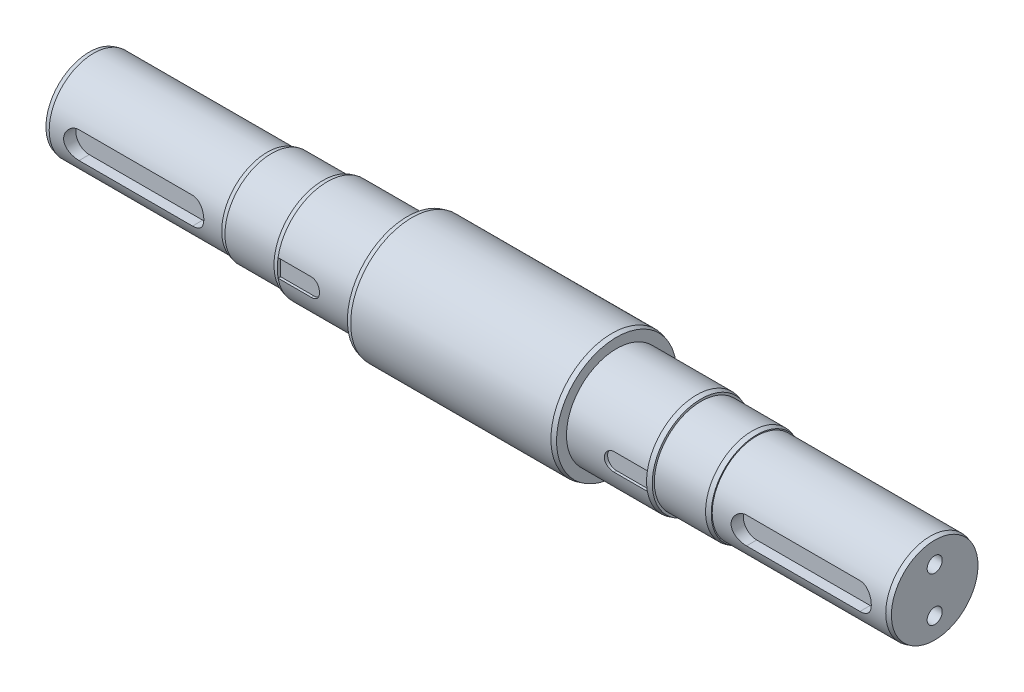
SolidWorks part; units mm, degrees
ref_plane "Ebene vorne" through (0, 0, 0) normal (0, 0, 1) x (1, 0, 0)
ref_plane "Ebene oben" through (0, 0, 0) normal (0, 1, 0) x (1, 0, 0)
ref_plane "Ebene rechts" through (0, 0, 0) normal (1, 0, 0) x (0, 0, -1)
sketch "Skizze1" plane through (0, 0, 0) normal (0, 0, 1) x (1, 0, 0)
  line L0 (-55.0769, 0) -> (85.8247, 0) construction
  line L1 (-85, 22.5) -> (-70, 22.5)
  line L2 (0, 0) -> (0, 27.5)
  line L3 (0, 27.5) -> (-47, 27.5)
  line L6 (-47, 27.5) -> (-47, 22.5)
  line L7 (-70, 22.5) -> (-47, 22.5)
  line L8 (-110, 20) -> (-110, 21)
  line L9 (-110, 21) -> (-85, 21)
  line L10 (-110, 20) -> (-190, 20)
  line L11 (-190, 20) -> (-190, 0)
  line L12 (-190, 0) -> (0, 0)
  line L13 (-85, 21) -> (-85, 22.5)
  point P3 (-150, 20)
  dimension "D1" = 23
  dimension "D2" = 40
  dimension "D3" = 42
  dimension "D8" = 80
  dimension "D9" = 25
  dimension "D10" = 15
revolve "Rotation1" add sketch "Skizze1" angle 360 about L0
chamfer "Fase1" distance 2 angle 15 3 edges at (-47, 0, 27.5) (-85, 0, 22.5) (-110, 0, 21)
ref_plane "Ebene1" through (0, 0, 20) normal (0, 0, 1) x (1, 0, 0)
sketch "Skizze2" plane through (0, 0, 20) normal (0, 0, 1) x (1, 0, 0)
  line L0 (-110, 0) -> (-190, 0) construction
  line L1 (-190, 20) -> (-190, -20) construction
  line L2 (-175.5, 6) -> (-124.5, 6)
  line L4 (-124.5, -6) -> (-175.5, -6)
  arc A0 (-175.5, -6) -> (-175.5, 6) centre (-175.5, 0) cw
  arc A1 (-124.5, 6) -> (-124.5, -6) centre (-124.5, 0) cw
  dimension "D1" = 6
  dimension "D4" = 6
  dimension "D5" = 51
  dimension "D6" = 14.5
  dimension "D2" = 12
  dimension "D3" = 6
extrude "Schnitt-Linear austragen1" cut sketch "Skizze2" against normal blind 5.5
ref_plane "Ebene2" through (0, 0, 22.5) normal (0, 0, 1) x (1, 0, 0)
sketch "Skizze3" plane through (-190, 0, 0) normal (-1, 0, 0) x (0, 0, 1)
  line L0 (0, 36.2616) -> (0, -42.0689) construction
  point P3 (0, 10)
  point P4 (0, -10)
  dimension "D1" = 10
  dimension "D2" = 10
hole_wizard "M8 Gewindebohrung1" positions "Skizze7" profile "Skizze6" tap size "M8" standard "DIN"
sketch "Skizze7" plane through (-190, 0, 0) normal (-1, 0, 0) x (0, 0, 1)
  point P0 (0, 10)
  point P3 (0, -10)
sketch "Skizze6" plane through (-190, 10, 0) normal (0, 1, 0) x (0, 0, 1)
  line L0 (0, 0) -> (0, 22.0429)
  line L1 (0, 22.0429) -> (3.4, 20)
  line L2 (3.4, 20) -> (3.4, 0)
  line L5 (3.4, 0) -> (0, 0)
  line L10 (0, 22.0429) -> (-3.4, 20) construction
  line L11 (0, -6.35) -> (0, 107.95) construction
  dimension "Bohrerdurchmesser" = 6.8
  dimension "Bohrungstiefe" = 20
  dimension "Spitzenwinkel" = 118
cosmetic thread "Bohrungsgewinde3" parameters "D1"=15, "D2"=8
cosmetic thread "Bohrungsgewinde4" parameters "D1"=15, "D2"=8
chamfer "Fase2" distance 2 angle 15 1 edges at (-190, 0, 20)
sketch "Skizze8" plane through (0, 0, 22.5) normal (0, 0, 1) x (1, 0, 0)
  line L1 (-83, 22.5) -> (-83, -22.5) construction
  line L2 (-83, 4) -> (-68, 4)
  line L4 (-47, 0) -> (-83, 0) construction
  line L5 (-68, -4) -> (-83, -4)
  line L6 (-83, 4) -> (-83, -4)
  arc A0 (-68, -4) -> (-68, 4) centre (-68, 0) ccw
  dimension "D1" = 8
  dimension "D2" = 15
extrude "Schnitt-Linear austragen2" cut sketch "Skizze8" against normal blind 1.5
mirror "Spiegeln1" about plane through (0, 0, 0) normal (-1, 0, 0) of bodies 106
